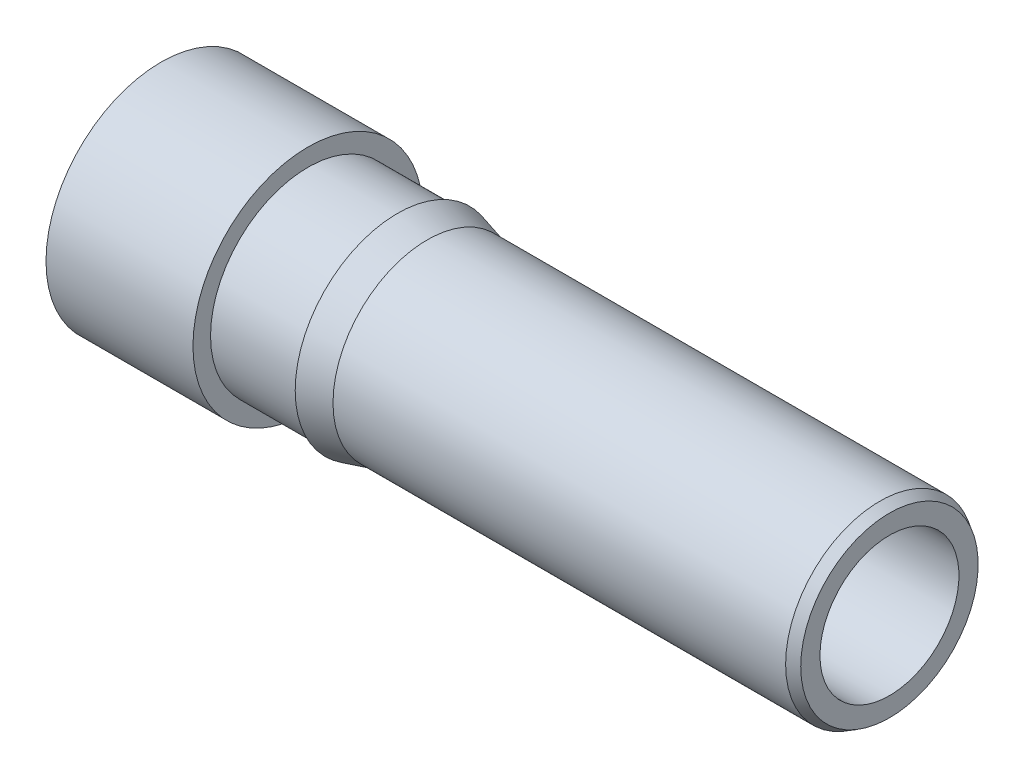
SolidWorks part; units mm, degrees
material "Brass Alloy 385"
ref_plane "Front Plane" through (0, 0, 0) normal (0, 0, 1) x (1, 0, 0)
ref_plane "Top Plane" through (0, 0, 0) normal (0, 1, 0) x (1, 0, 0)
ref_plane "Right Plane" through (0, 0, 0) normal (1, 0, 0) x (0, 0, -1)
sketch "Sketch1" plane through (0, 0, 0) normal (0, 0, 1) x (1, 0, 0)
  line L0 (0, 0) -> (0, 0.9144)
  line L1 (0, 0.9144) -> (1.1684, 0.9144)
  line L2 (1.1684, 0.9144) -> (1.1684, 0.7747)
  line L3 (1.1684, 0.7747) -> (1.8796, 0.7747)
  line L4 (1.8796, 0.7747) -> (1.8796, 0.8128)
  line L5 (1.8796, 0.8128) -> (2.1166, 0.7493)
  line L6 (2.1166, 0.7493) -> (5.715, 0.7493)
  line L7 (5.715, 0.7493) -> (5.7912, 0.7053)
  line L8 (5.7912, 0.7053) -> (5.7912, 0)
  line L9 (0, 0) -> (5.7912, 0)
  line L10 (0, 0) -> (5.7912, 0) construction
revolve "RevolutionAngle1" add sketch "Sketch1" angle 360 about L10
hole_wizard "Hole1" positions "Sketch3" profile "Sketch2" legacy
sketch "Sketch3" plane through (0, 0, 0) normal (-1, 0, 0) x (0, 0, 1)
  point P0 (0, 0)
sketch "Sketch2" plane through (0, 0, 0) normal (0, 1, 0) x (0, 0, 1)
  line L0 (0, 0) -> (0, 3.4118)
  line L1 (0, 3.4118) -> (0.6477, 3.0226)
  line L2 (0.6477, 3.0226) -> (0.6477, 0)
  line L4 (0.6477, 0) -> (0, 0)
  line L6 (0, 3.4118) -> (-0.6477, 3.0226) construction
  line L7 (0, -4.2442) -> (0, 117.3081) construction
  dimension "A" = 1.2954
  dimension "N" = 3.0226
  dimension "Drill Angle" = 118
hole_wizard "Hole2" positions "Sketch5" profile "Sketch4" legacy end condition through all
sketch "Sketch5" plane through (0, 0.1895, -0.7943) normal (-1, 0, 0) x (0, 0, 1)
  point P0 (0.7943, -0.1895)
sketch "Sketch4" plane through (0, 0, 0) normal (0, 1, 0) x (0, 0, 1)
  line L0 (0, 0) -> (0, 6.1231)
  line L1 (0, 6.1231) -> (0.5524, 5.7912)
  line L2 (0.5524, 5.7912) -> (0.5524, 0)
  line L4 (0.5524, 0) -> (0, 0)
  line L6 (0, 6.1231) -> (-0.5524, 5.7912) construction
  line L7 (0, -4.2442) -> (0, 117.3081) construction
  dimension "A2" = 1.1049
  dimension "REF" = 5.7912
  dimension "Drill Angle" = 118
